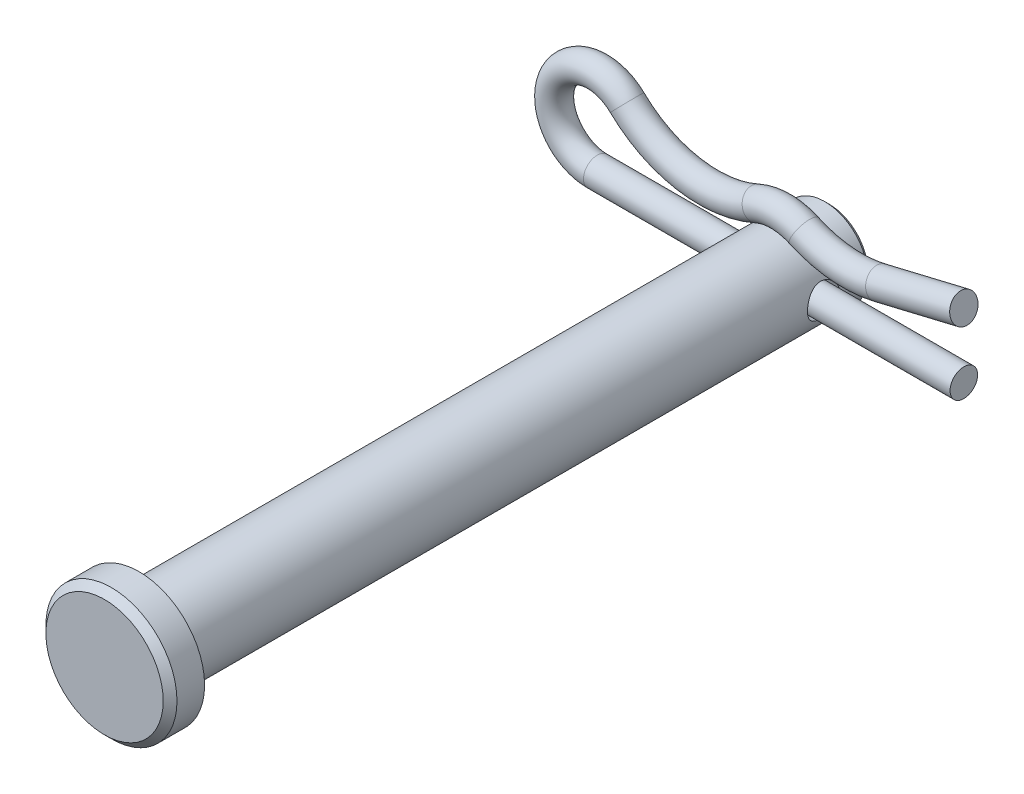
SolidWorks part; units mm, degrees
ref_plane "Front" through (0, 0, 0) normal (0, 0, 1) x (1, 0, 0)
ref_plane "Top" through (0, 0, 0) normal (0, 1, 0) x (1, 0, 0)
ref_plane "Right" through (0, 0, 0) normal (1, 0, 0) x (0, 0, -1)
sketch "Sketch1" plane through (0, 0, 0) normal (0, 0, 1) x (1, 0, 0)
  circle A0 centre (0, 0) radius 3.175
  point P3 (0, 3.175)
  point P4 (0, -3.175)
  dimension "dia" = 6.35
extrude "Extrude1" add sketch "Sketch1" along normal mid plane 50.8
sketch "Sketch2" plane through (0, 0, 25.4) normal (0, 0, 1) x (1, 0, 0)
  circle A0 centre (0, 0) radius 4.826
  dimension "head dia" = 9.652
extrude "Extrude2" add sketch "Sketch2" along normal blind 2.54
chamfer "Chamfer1" distance 0.508 angle 45 1 edges at (4.826, 0, 27.94)
sketch "Sketch3" plane through (0, 0, 0) normal (1, 0, 0) x (0, 0, -1)
  line L0 (-25.4, -3.175) -> (-25.4, 3.175) construction
  circle A0 centre (21.8281, 0) radius 1.1906
  point P2 (20.6375, 0)
  dimension "hole dia" = 2.3813
  dimension "useable Lg" = 46.0375
extrude "Extrude3" cut sketch "Sketch3" against normal through all and the other way through all
chamfer "Chamfer2" distance 0.3175 angle 45 1 edges at (3.175, 0, -25.4)
ref_plane "Plane1" through (0, 0, -21.8281) normal (0, 0, 1) x (1, 0, 0)
sketch "Sketch6" plane through (0, 0, -21.8281) normal (0, 0, 1) x (1, 0, 0)
  line L0 (13.4937, 0) -> (-13.4937, 0)
  line L1 (7.306, 3.2847) -> (13.4937, 4.7625)
  line L2 (-13.4937, 3.175) -> (-13.4937, 6.35) construction
  arc A0 (-13.4937, 0) -> (-11.293, 5.4635) centre (-13.4937, 3.175) cw
  arc A1 (1.7284, 3.818) -> (-1.7284, 3.818) centre (0, 0) ccw
  circle A2 centre (0, 0) radius 1.016 construction
  arc A3 (-1.7284, 3.818) -> (-11.293, 5.4635) centre (-5.2963, 11.6993) cw
  circle A4 centre (0, 4.191) radius 1.016 construction
  circle A5 centre (0, 0) radius 3.175 construction
  arc A6 (1.7284, 3.818) -> (7.306, 3.2847) centre (5.2963, 11.6993) ccw
  point P2 (-5.2963, 3.048)
  point P9 (-13.4937, 4.7625)
  point P18 (-16.6687, 3.175)
  point P22 (-13.4937, 6.35)
  point P23 (0, 1.016)
  dimension "D2" = 6.35
  dimension "pin dia" = 2.032
  dimension "D1" = 3.048
  dimension "pin Lg" = 30.1625
ref_plane "Plane2" through (13.4937, 0, -21.8281) normal (-1, 0, 0) x (0, 0, 1)
sketch "Sketch7" plane through (13.4937, 0, -21.8281) normal (-1, 0, 0) x (0, 0, 1)
  circle A0 centre (0, 0) radius 1.016
sweep "Sweep1" add profiles "Sketch7" path "Sketch6"
sketch "Sketch8" plane through (0, 0, 0) normal (1, 0, 0) x (0, 0, -1)
  line L0 (-27.94, 4.318) -> (-27.94, -4.318) construction
  line L1 (-27.432, -4.826) -> (-25.4, -4.826) construction
  line L2 (25.4, -2.8575) -> (25.4, 2.8575) construction
  line L3 (20.6375, 7.366) -> (21.8281, 7.366) construction
  line L4 (21.8281, 3.175) -> (21.8281, 6.35) construction
  arc A0 (22.8441, 6.35) -> (20.8121, 6.35) centre (21.8281, 6.35) ccw construction
  point P0 (-27.94, 4.826)
  point P1 (-25.4, 4.826)
  point P5 (25.4, 3.175)
  point P8 (-27.94, -4.826)
  point P9 (25.4, -3.175)
  point P12 (20.6375, 7.366)
equation "\"D1@Chamfer1\" = \"head ht@Extrude2\" * .2"
equation "\"D1@Chamfer2\" = \"dia@Sketch1\" * .05"
equation "\"D2@Sketch6\" = \"dia@Sketch1\" * 1"
equation "\"D1@Sketch6\" = \"pin dia@Sketch6\" * 1.5"
